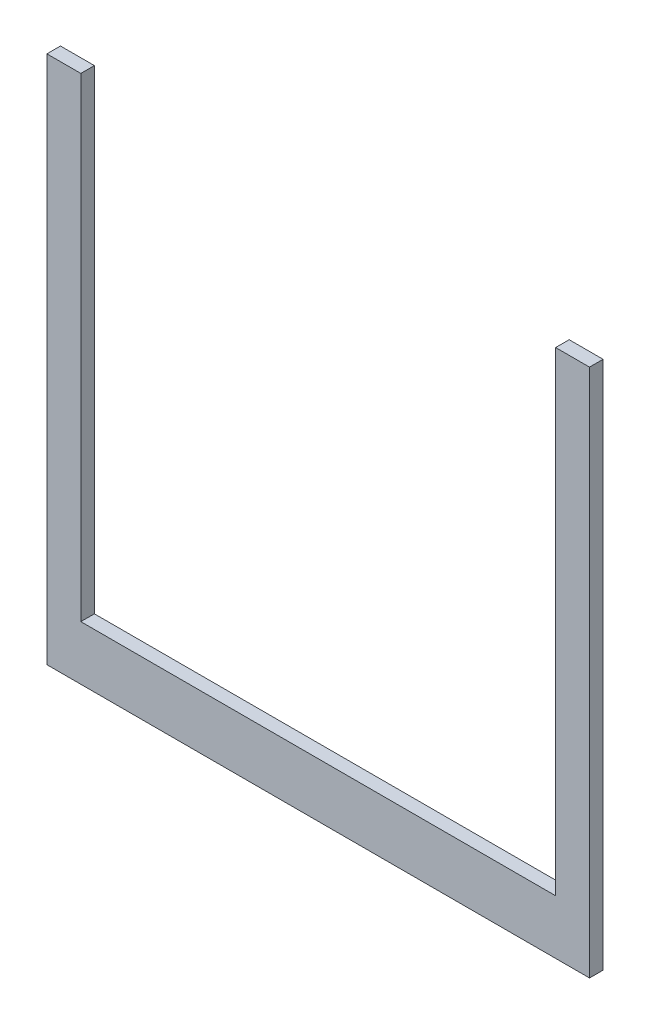
SolidWorks part; units mm, degrees
material "Oak"
ref_plane "Front Plane" through (0, 0, 0) normal (0, 0, 1) x (1, 0, 0)
ref_plane "Top Plane" through (0, 0, 0) normal (0, 1, 0) x (1, 0, 0)
ref_plane "Right Plane" through (0, 0, 0) normal (1, 0, 0) x (0, 0, -1)
sketch "Sketch1" plane through (0, 0, 0) normal (0, 0, 1) x (1, 0, 0)
  line L0 (0, 390) -> (25, 390)
  line L1 (25, 390) -> (25, 40)
  line L2 (25, 40) -> (375, 40)
  line L3 (375, 40) -> (375, 390)
  line L4 (375, 390) -> (400, 390)
  line L5 (400, 390) -> (400, 0)
  line L6 (400, 0) -> (0, 0)
  line L7 (0, 0) -> (0, 390)
  dimension "D1" = 25
  dimension "D2" = 400
  dimension "D3" = 350
  dimension "D4" = 390
extrude "Boss-Extrude1" add sketch "Sketch1" along normal blind 10
